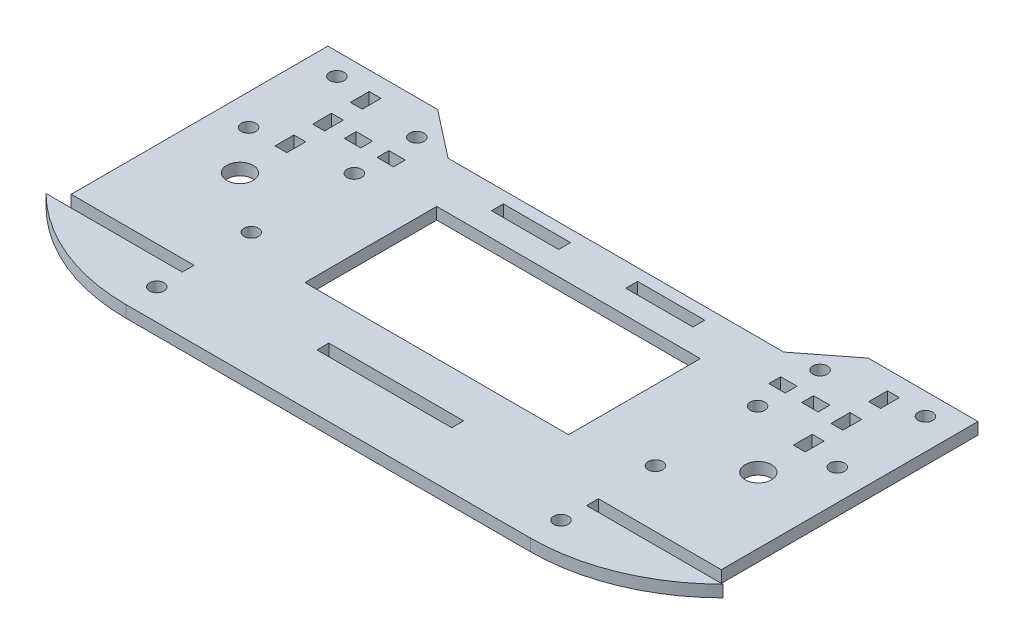
SolidWorks part; units mm, degrees
ref_plane "Ön Düzlem" through (0, 0, 0) normal (0, 0, 1) x (1, 0, 0)
ref_plane "Üst Düzlem" through (0, 0, 0) normal (0, 1, 0) x (1, 0, 0)
ref_plane "Sağ Düzlem" through (0, 0, 0) normal (1, 0, 0) x (0, 0, -1)
sketch "Sketch1" plane through (0, 0, 0) normal (0, 1, 0) x (1, 0, 0)
  line L1 (-46, 0) -> (46, 0)
  line L21 (73.9952, 35.5) -> (73.9952, 15.5)
  line L22 (-15.34, 15.5) -> (-15.34, 12.8)
  line L23 (-46.0152, 15.5) -> (-46.0152, 12.8)
  line L24 (-15.34, 12.8) -> (15.34, 12.8)
  line L25 (15.34, 12.8) -> (15.34, 15.5)
  line L26 (15.34, 15.5) -> (-15.34, 15.5)
  line L29 (46.0152, 15.5) -> (46.0152, 12.8)
  line L31 (46.0152, 15.5) -> (73.9952, 15.5)
  line L32 (77.0252, 12.8) -> (46.0152, 12.8)
  line L33 (-46.0152, 15.5) -> (-73.9952, 15.5)
  line L34 (-46.0152, 12.8) -> (-77.0252, 12.8)
  line L39 (-38.2, 65.5) -> (38.2, 65.5)
  line L45 (-22.92, 62.8) -> (-7.64, 62.8)
  line L47 (7.64, 62.8) -> (22.92, 62.8)
  line L48 (38.2, 65.5) -> (48.9952, 73.92)
  line L49 (22.92, 60.1) -> (7.64, 60.1)
  line L51 (-7.64, 60.1) -> (-22.92, 60.1)
  line L53 (-22.92, 62.8) -> (-22.92, 60.1)
  line L54 (-7.64, 62.8) -> (-7.64, 60.1)
  line L55 (7.64, 62.8) -> (7.64, 60.1)
  line L56 (22.92, 62.8) -> (22.92, 60.1)
  line L81 (73.9952, 35.5) -> (73.9952, 43.92)
  line L83 (68.9952, 73.92) -> (73.9952, 73.92)
  line L84 (60.3452, 56.8171) -> (57.6452, 56.8171)
  line L85 (57.6452, 56.8171) -> (57.6452, 61.1028)
  line L86 (42.7252, 57.578) -> (42.7252, 60.278)
  line L87 (68.9952, 73.92) -> (48.9952, 73.92)
  line L88 (42.7252, 57.578) -> (46.4552, 57.578)
  line L89 (57.6452, 48.2457) -> (57.6452, 52.5314)
  line L90 (57.6452, 52.5314) -> (60.3452, 52.5314)
  line L91 (60.3452, 65.3885) -> (57.6452, 65.3885)
  line L93 (46.4552, 57.578) -> (46.4552, 60.278)
  line L94 (68.9952, 73.92) -> (48.9952, 43.92) construction
  line L95 (50.1852, 60.294) -> (53.9152, 60.294)
  line L96 (60.3452, 56.8171) -> (60.3452, 61.1028)
  line L97 (57.6452, 69.6743) -> (60.3452, 69.6743)
  line L99 (57.6452, 61.1028) -> (60.3452, 61.1028)
  line L103 (57.6452, 65.3885) -> (57.6452, 69.6743)
  line L104 (50.1852, 57.594) -> (53.9152, 57.594)
  line L105 (68.9952, 43.92) -> (48.9952, 73.92) construction
  line L106 (57.6452, 48.2457) -> (60.3452, 48.2457)
  line L107 (50.1852, 60.294) -> (50.1852, 57.594)
  line L108 (60.3452, 48.2457) -> (60.3452, 52.5314)
  line L109 (42.7252, 60.278) -> (46.4552, 60.278)
  line L110 (60.3452, 65.3885) -> (60.3452, 69.6743)
  line L111 (73.9952, 73.92) -> (73.9952, 43.92)
  line L112 (53.9152, 60.294) -> (53.9152, 57.594)
  line L114 (-73.9952, 15.5) -> (-73.9952, 73.92)
  line L115 (-53.9152, 60.294) -> (-53.9152, 57.594)
  line L116 (-50.1852, 60.294) -> (-50.1852, 57.594)
  line L117 (-46.4552, 57.578) -> (-46.4552, 60.278)
  line L118 (-42.7252, 57.578) -> (-42.7252, 60.278)
  line L119 (-50.1852, 57.594) -> (-53.9152, 57.594)
  line L120 (-42.7252, 57.578) -> (-46.4552, 57.578)
  line L121 (-50.1852, 60.294) -> (-53.9152, 60.294)
  line L123 (-42.7252, 60.278) -> (-46.4552, 60.278)
  line L124 (-57.6452, 69.6743) -> (-60.3452, 69.6743)
  line L125 (-60.3452, 65.3885) -> (-57.6452, 65.3885)
  line L126 (-57.6452, 61.1028) -> (-60.3452, 61.1028)
  line L127 (-60.3452, 56.8171) -> (-57.6452, 56.8171)
  line L128 (-57.6452, 52.5314) -> (-60.3452, 52.5314)
  line L129 (-57.6452, 48.2457) -> (-60.3452, 48.2457)
  line L131 (-57.6452, 65.3885) -> (-57.6452, 69.6743)
  line L132 (-57.6452, 56.8171) -> (-57.6452, 61.1028)
  line L133 (-68.9952, 73.92) -> (-73.9952, 73.92)
  line L134 (-57.6452, 48.2457) -> (-57.6452, 52.5314)
  line L135 (-60.3452, 65.3885) -> (-60.3452, 69.6743)
  line L136 (-60.3452, 56.8171) -> (-60.3452, 61.1028)
  line L139 (-60.3452, 48.2457) -> (-60.3452, 52.5314)
  line L140 (-68.9952, 73.92) -> (-48.9952, 73.92)
  line L142 (-38.2, 65.5) -> (-48.9952, 73.92)
  line L144 (30, 24.71) -> (-30, 24.71)
  line L145 (30, 24.71) -> (30, 54.71)
  line L146 (30, 54.71) -> (-30, 54.71)
  line L147 (-30, 24.71) -> (-30, 54.71)
  arc A0 (-77.0252, 12.8) -> (-46, 0) centre (-46, 44) ccw
  arc A1 (46, 0) -> (77.0252, 12.8) centre (46, 44) ccw
  circle A2 centre (46, 28.5) radius 1.65
  circle A3 centre (46, 7) radius 1.65
  circle A4 centre (-46, 7) radius 1.65
  circle A5 centre (-46, 28.5) radius 1.65
  circle A10 centre (66.9952, 68.96) radius 1.65
  circle A11 centre (66.9952, 48.88) radius 1.65
  circle A12 centre (45.8923, 66.0768) radius 1.65
  circle A13 centre (45.8923, 51.8431) radius 1.65
  circle A14 centre (-66.9952, 48.88) radius 1.65
  circle A15 centre (-45.8923, 66.0768) radius 1.65
  circle A16 centre (-66.9952, 68.96) radius 1.65
  circle A17 centre (-45.8923, 51.8431) radius 1.65
  circle A18 centre (-58.9952, 38.92) radius 3
  circle A19 centre (58.9952, 38.92) radius 3
  point P76 (58.9952, 58.92)
  point P181 (-58.9952, 58.92)
  dimension "D1" = 60
  dimension "D2" = 30
  dimension "D3" = 30
  dimension "D4" = 20
extrude "Boss-Extrude1" add sketch "Sketch1" along normal blind 2.7
